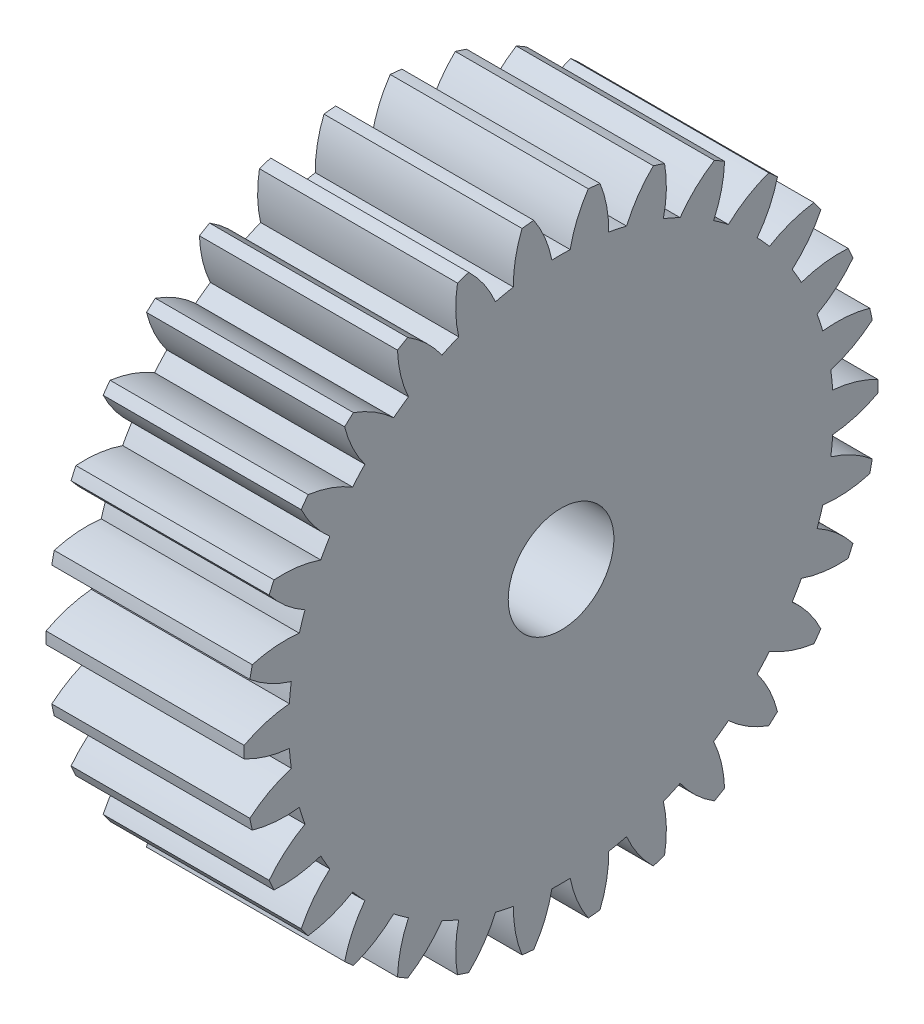
SolidWorks part; units mm, degrees
ref_plane "Plane1" through (0, 0, 0) normal (0, 0, 1) x (1, 0, 0)
ref_plane "Plane2" through (0, 0, 0) normal (0, 1, 0) x (1, 0, 0)
ref_plane "Plane3" through (0, 0, 0) normal (1, 0, 0) x (0, 0, -1)
other "Configuration Table"
sketch "HoldingSke" plane through (0, 0, 0) normal (0, 1, 0) x (1, 0, 0)
  line L0 (0, 0) -> (0.5774, -0.3333)
  line L1 (-15, 0) -> (100, 0) construction
  line L2 (0, 0) -> (-2.1039, 2.3779)
  line L3 (0, 0) -> (-11.863, 4.5341)
  line L4 (0, 0) -> (7.479, 4.318)
  line L5 (0, 0) -> (-46.8476, -17.4728)
  line L6 (0, 0) -> (-12.4344, -8.3896)
  line L7 (-2.1039, 2.3779) -> (8.6586, 51.2059)
  line L8 (-76.2, 54.61) -> (-74.8, 54.61)
  line L9 (-71.009, 38.7566) -> (-53.1078, 45.2721)
  line L10 (-76.2, 71.12) -> (104.1128, 71.12)
  line L11 (0, 0) -> (-15, 0)
  line L12 (-76.2, 101.6) -> (-76.147, 101.6)
  line L13 (24.9733, 27.94) -> (52.9518, 28.4284)
  line L14 (24.9733, 27.94) -> (24.9743, 27.94)
  line L15 (24.9733, 27.94) -> (100.4006, 29.5858)
  line L16 (-63.627, -1.5) -> (-12.827, -1.5)
  circle A0 centre (0, 0) radius 4
  circle A1 centre (0, 0) radius 20.624
  circle A2 centre (0, 0) radius 37.5
  circle A3 centre (0, 0) radius 4
  dimension "MHD" = 41.248
  dimension "Hub_dia" = 75
  dimension "Bore" = 8
  dimension "MBD" = 8
  dimension "Num_teeth" = 30
  dimension "Pitch" = 0.6667
  dimension "Overall_len" = 50
  dimension "Show_teeth" = 30
  dimension "Thickness" = 15
  dimension "OAL" = 50.0001
  dimension "T_dim" = 1.4
  dimension "Ap" = 20
  dimension "H" = 19.05
  dimension "Pitch_radius" = 180.3128
  dimension "Width" = 15
  dimension "Backlash" = 0.053
  dimension "Addendum_fac" = 1
  dimension "Dedendum_fac" = 1.25
  dimension "Clearance_fac" = 0.25
  dimension "Dedendum_add" = 0.001
  dimension "Module" = 1.5
sketch "BasProSke" plane through (0, 0, 0) normal (0, 1, 0) x (1, 0, 0)
  line L0 (-10, 0) -> (60, 0) construction
  line L1 (0, 0) -> (0, 24)
  line L2 (0, 0) -> (15, 0)
  line L3 (15, 0) -> (15, 24)
  line L4 (15, 24) -> (0, 24)
  dimension "Thickness" = 15
  dimension "Diameter" = 48
revolve "Base-Revolve" add sketch "BasProSke" angle 360 about L0
sketch "TooCutSke" plane through (0, 0, 0) normal (1, 0, 0) x (0, 0, -1)
  line L1 (0, 0) -> (0, 107) construction
  line L2 (0, 0) -> (-1.2703, 22.4641) construction
  line L3 (0, 0) -> (-4.6983, 44.7014) construction
  line L4 (-1.2703, 22.4641) -> (-2.3492, 22.3507) construction
  arc A0 (0.6933, 20.6123) -> (-0.6933, 20.6123) centre (0, 0) ccw
  arc A1 (2.0805, 23.9351) -> (-2.0805, 23.9351) centre (0, 0) ccw
  circle A2 centre (0, 0) radius 22.5 construction
  circle A3 centre (0, 0) radius 21.1431 construction
  arc A4 (-0.6933, 20.6123) -> (-2.0805, 23.9351) centre (-9.5243, 18.8764) ccw
  arc A5 (2.0805, 23.9351) -> (0.6933, 20.6123) centre (9.5243, 18.8764) ccw
  dimension "Root_dia" = 41.248
  dimension "Overcut_dia" = 48.0508
  dimension "Pitch_dia" = 45
  dimension "Base_dia" = 42.2862
  dimension "Flank_rad" = 9
  dimension "Half_ang" = 6
  dimension "Half_CT" = 1.0848
extrude "ToothCut" cut sketch "TooCutSke" along normal through all
fillet "Breaks" [suppressed] radius 0.03
fillet "RootFillets" [suppressed] radius 0.376
pattern_circular "TeethCuts" count 30 every 12 about axis through (-10, 0, 0) along (1, 0, 0) of "ToothCut", "RootFillets", "Breaks"
sketch "HubNeaOneSke" plane through (0, 0, 0) normal (-1, 0, 0) x (0, 0, 1)
  circle A0 centre (0, 0) radius 20.624
  dimension "Diameter" = 41.248
extrude "HubNearOne" [suppressed] add sketch "HubNeaOneSke" along normal blind 35.0001
sketch "HubNeaBotSke" plane through (0, 0, 0) normal (-1, 0, 0) x (0, 0, 1)
  circle A0 centre (0, 0) radius 20.624
  dimension "Diameter" = 41.248
extrude "HubNearBoth" [suppressed] add sketch "HubNeaBotSke" along normal blind 17.5
ref_plane "FarPln" through (15, 0, 0) normal (1, 0, 0) x (0, 0, -1)
sketch "HubFarSke" plane through (15, 0, 0) normal (1, 0, 0) x (0, 0, -1)
  circle A0 centre (0, 0) radius 20.624
  dimension "Diameter" = 41.248
extrude "HubFar" [suppressed] add sketch "HubFarSke" along normal blind 17.5
sketch "BorSke" plane through (0, 0, 0) normal (1, 0, 0) x (0, 0, -1)
  circle A0 centre (0, 0) radius 4
  dimension "Diameter" = 8
extrude "Bore" cut sketch "BorSke" along normal mid plane 100.0001
sketch "KeySke" plane through (0, 0, 0) normal (1, 0, 0) x (0, 0, -1)
  line L0 (-1.5, 0) -> (-1.5, 5.4)
  line L1 (-1.5, 5.4) -> (1.5, 5.4)
  line L2 (1.5, 5.4) -> (1.5, 0)
  line L3 (0, 0) -> (0, 34) construction
  line L4 (-1.5, 0) -> (1.5, 0)
  dimension "Offset" = 5.4
  dimension "Width" = 3
extrude "Keyway" [suppressed] cut sketch "KeySke" along normal mid plane 100.0001
pattern_circular "Keyway2" [suppressed] count 2 every 90 about axis through (-10, 0, 0) along (1, 0, 0)
equation "' \"Module@HoldingSke\" = 6.35"
equation "' \"Num_teeth@HoldingSke\" = 12"
equation "' \"Ap@HoldingSke\" =  20"
equation "' \"Ap@HoldingSke\" = 20"
equation "' \"Width@HoldingSke\" = 0.5 * 25.4"
equation "' \"Hub_dia@HoldingSke\"= 1 * 25.4"
equation "' \"Hub_dia@HoldingSke\" = 1 * 25.4"
equation "' \"Overall_len@HoldingSke\" = 1.0 * 25.4"
equation "' \"Bore@HoldingSke\" = 0.75 * 25.4"
equation "' \"T_dim@HoldingSke\" = 0.1 * 25.4"
equation "' \"Width@KeySke\" = 0.25 * 25.4"
equation "' \"Show_teeth@HoldingSke\" = 13"
equation "' \"Backlash@HoldingSke\" = 0.009 * 25.4"
equation "' \"Addendum_fac@HoldingSke\" = 1.0"
equation "' \"Dedendum_fac@HoldingSke\" = 1.25"
equation "' \"Dedendum_add@HoldingSke\" = 0.00005 * 25.4"
equation "' \"Clearance_fac@HoldingSke\" = 0.25"
equation "\"Pitch@HoldingSke\" = 1 / \"Module@HoldingSke\""
equation "\"Overcut_dia@TooCutSke\" = (\"Num_teeth@HoldingSke\" + 2 * \"Addendum_fac@HoldingSke\") / \"Pitch@HoldingSke\" + 0.002 * 25.4"
equation "\"Pitch_dia@TooCutSke\" = \"Num_teeth@HoldingSke\" / \"Pitch@HoldingSke\""
equation "\"Base_dia@TooCutSke\" = \"Num_teeth@HoldingSke\" / \"Pitch@HoldingSke\" * cos((\"Ap@HoldingSke\"  * 3.14159265 / 180))"
equation "\"Root_dia@TooCutSke\" = (\"Num_teeth@HoldingSke\" + 2) / \"Pitch@HoldingSke\" - 2 * (\"Addendum_fac@HoldingSke\" + \"Dedendum_fac@HoldingSke\") / \"Pitch@HoldingSke\" - \"Dedendum_add@HoldingSke\" * 2"
equation "\"Half_ang@TooCutSke\" = 180 / \"Num_teeth@HoldingSke\""
equation "\"Half_CT@TooCutSke\" = \"Num_teeth@HoldingSke\" / \"Pitch@HoldingSke\" * sin((3.14159265 / 2 / \"Num_teeth@HoldingSke\")) / 2 - 7 * \"Backlash@HoldingSke\" / 4"
equation "\"Flank_rad@TooCutSke\" = \"Num_teeth@HoldingSke\" / \"Pitch@HoldingSke\" / 5"
equation "\"Radius@RootFillets\" = \"Clearance_fac@HoldingSke\" / \"Pitch@HoldingSke\" + \"Dedendum_add@HoldingSke\""
equation "\"Break_rad@Breaks\" = 0.02 / \"Pitch@HoldingSke\""
equation "\"Thickness@HoldingSke\" = \"Width@HoldingSke\""
equation "\"OAL@HoldingSke\" = \"Thickness@HoldingSke\""
equation "\"MHD@HoldingSke\" = (\"Num_teeth@HoldingSke\" + 2) / \"Pitch@HoldingSke\" - 2 * (\"Addendum_fac@HoldingSke\" + \"Dedendum_fac@HoldingSke\")  / \"Pitch@HoldingSke\" - \"Dedendum_add@HoldingSke\" * 2"
equation "\"MBD@HoldingSke\" = (\"Num_teeth@HoldingSke\" + 2) / \"Pitch@HoldingSke\" - 2 * (\"Addendum_fac@HoldingSke\" + \"Dedendum_fac@HoldingSke\")  / \"Pitch@HoldingSke\" - \"Dedendum_add@HoldingSke\" * 2 - 0.002 * 25.4"
equation "\"MHD@HoldingSke\" = ((sgn( \"MHD@HoldingSke\" - \"Hub_dia@HoldingSke\" )-1)*( \"MHD@HoldingSke\" - \"Hub_dia@HoldingSke\" ))/-2+ \"Hub_dia@HoldingSke\""
equation "\"MBD@HoldingSke\" = ((sgn( \"MBD@HoldingSke\" - \"Bore@HoldingSke\" )-1)*( \"MBD@HoldingSke\" - \"Bore@HoldingSke\" ))/-2+ \"Bore@HoldingSke\""
equation "\"OAL@HoldingSke\" = ((sgn( \"OAL@HoldingSke\" - \"Overall_len@HoldingSke\" )+1)*( \"OAL@HoldingSke\" - \"Overall_len@HoldingSke\" ))/2 + \"Overall_len@HoldingSke\" + 0.000002 * 25.4"
equation "\"Num_teeth@TeethCuts\" = int( \"Show_teeth@HoldingSke\" ) + 1"
equation "\"Num_teeth@TeethCuts\" = ((sgn( \"Num_teeth@TeethCuts\" - \"Num_teeth@HoldingSke\" )-1)*( \"Num_teeth@TeethCuts\" - \"Num_teeth@HoldingSke\" ))/-2+ \"Num_teeth@HoldingSke\""
equation "\"Num_teeth@TeethCuts\" = ((sgn( \"Num_teeth@TeethCuts\" - 2.0)+1)*( \"Num_teeth@TeethCuts\" - 2.0))/2 +2.0"
equation "\"Angle@TeethCuts\" = 360.0 / \"Num_teeth@HoldingSke\""
equation "\"Diameter@BasProSke\" = (\"Num_teeth@HoldingSke\" + 2 * \"Addendum_fac@HoldingSke\") / \"Pitch@HoldingSke\""
equation "\"Thickness@BasProSke\"  = \"Thickness@HoldingSke\""
equation "' \"Fillet_rad@BasProSke\" =  \"Thickness@HoldingSke\" * 0.05"
equation "' \"Fillet_rad@BasProSke\" = \"Thickness@HoldingSke\" * 0.05"
equation "\"MHD@HoldingSke\" = ((sgn( \"MHD@HoldingSke\" - \"Root_dia@TooCutSke\" )-1)*( \"MHD@HoldingSke\" - \"Root_dia@TooCutSke\" ))/-2+ \"Root_dia@TooCutSke\""
equation "\"Diameter@HubNeaOneSke\" = \"MHD@HoldingSke\""
equation "\"Length@HubNearOne\" = \"OAL@HoldingSke\" - \"Thickness@BasProSke\""
equation "\"Diameter@HubNeaBotSke\" = \"MHD@HoldingSke\""
equation "\"Length@HubNearBoth\" = ( \"OAL@HoldingSke\" - \"Thickness@BasProSke\" ) / 2.0"
equation "\"Thickness@FarPln\" = \"Thickness@BasProSke\""
equation "\"Diameter@HubFarSke\" = \"MHD@HoldingSke\""
equation "\"Length@HubFar\" = ( \"OAL@HoldingSke\" - \"Thickness@BasProSke\" ) / 2.0"
equation "\"Diameter@BorSke\" = \"MBD@HoldingSke\""
equation "\"D1@Bore\" = \"OAL@HoldingSke\" * 2.0"
equation "\"D1@Keyway\" = \"OAL@HoldingSke\" * 2.0"
equation "\"Offset@KeySke\" = \"T_dim@HoldingSke\" + \"MBD@HoldingSke\" / 2.0"
